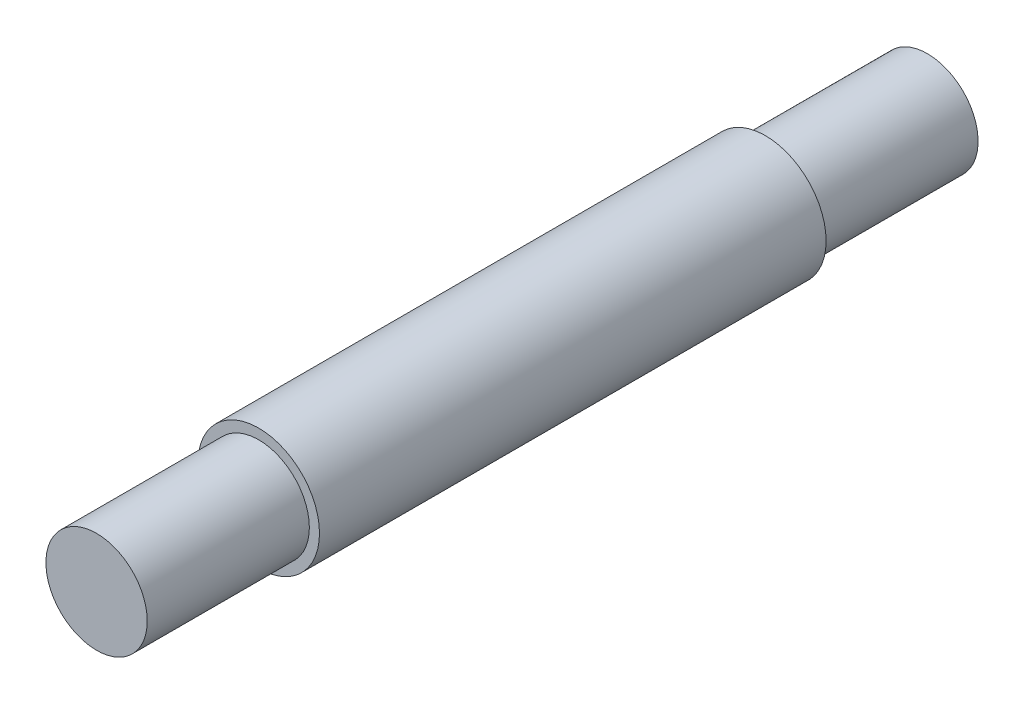
SolidWorks part; units mm, degrees
ref_plane "Ön Düzlem" through (0, 0, 0) normal (0, 0, 1) x (1, 0, 0)
ref_plane "Üst Düzlem" through (0, 0, 0) normal (0, 1, 0) x (1, 0, 0)
ref_plane "Sağ Düzlem" through (0, 0, 0) normal (1, 0, 0) x (0, 0, -1)
sketch "Çizim1" plane through (0, 0, 0) normal (0, 0, 1) x (1, 0, 0)
  circle A0 centre (0, 0) radius 6
  dimension "D1" = 12
extrude "Yükseklik-Ekstrüzyon1" add sketch "Çizim1" along normal blind 50
sketch "Çizim2" plane through (0, 0, 50) normal (0, 0, 1) x (1, 0, 0)
  circle A0 centre (0, 0) radius 5
  dimension "D1" = 10
extrude "Yükseklik-Ekstrüzyon2" add sketch "Çizim2" along normal blind 16
sketch "Çizim3" plane through (0, 0, 0) normal (0, 0, -1) x (-1, 0, 0)
  circle A0 centre (0, 0) radius 5
  dimension "D1" = 10
extrude "Yükseklik-Ekstrüzyon3" add sketch "Çizim3" along normal blind 16
